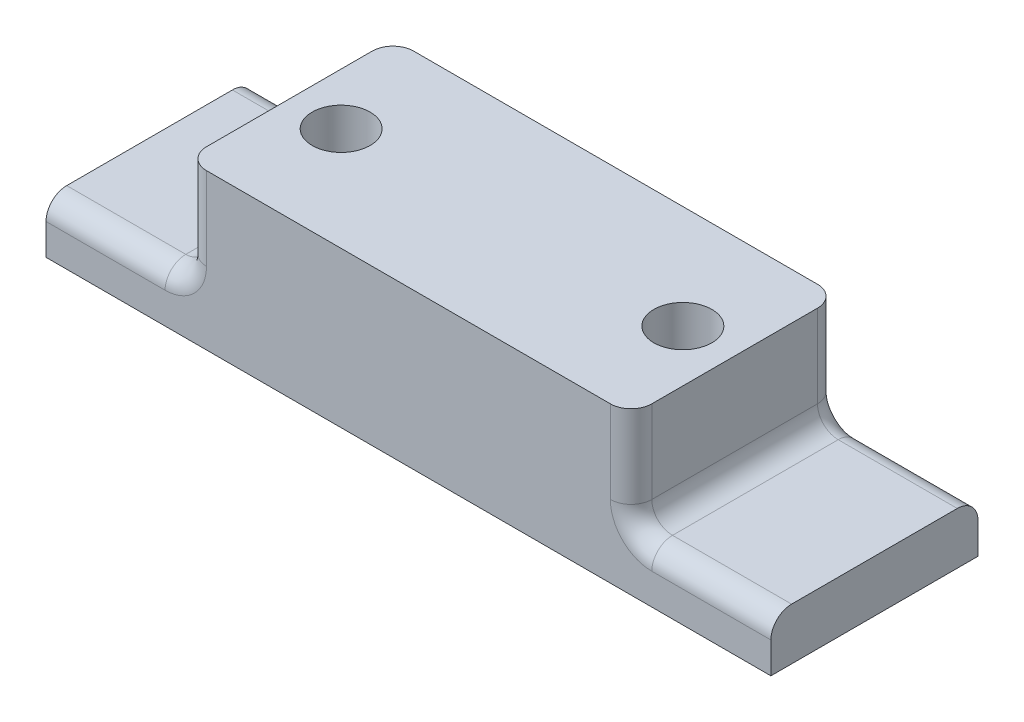
SolidWorks part; units mm, degrees
ref_plane "Front Plane" through (0, 0, 0) normal (0, 0, 1) x (1, 0, 0)
ref_plane "Top Plane" through (0, 0, 0) normal (0, 1, 0) x (1, 0, 0)
ref_plane "Right Plane" through (0, 0, 0) normal (1, 0, 0) x (0, 0, -1)
sketch "Sketch1" plane through (0, 0, 0) normal (0, 1, 0) x (1, 0, 0)
  line L0 (-29.7376, 16.1875) -> (-29.7376, -3.8125)
  line L1 (-29.7376, -3.8125) -> (40.2624, -3.8125)
  line L2 (40.2624, -3.8125) -> (40.2624, 16.1875)
  line L3 (40.2624, 16.1875) -> (-29.7376, 16.1875)
  dimension "D1" = 20
  dimension "D2" = 70
extrude "Boss-Extrude1" add sketch "Sketch1" along normal blind 5
sketch "Sketch2" plane through (0, 5, 0) normal (0, 1, 0) x (1, 0, 0)
  line L1 (-16.2376, 16.1875) -> (-16.2376, -3.8125)
  line L2 (40.2624, 16.1875) -> (-29.7376, 16.1875) construction
  line L3 (-29.7376, -3.8125) -> (40.2624, -3.8125) construction
  line L4 (-16.2376, -3.8125) -> (26.7624, -3.8125)
  line L5 (26.7624, -3.8125) -> (26.7624, 16.1875)
  line L6 (26.7624, 16.1875) -> (-16.2376, 16.1875)
  line L7 (-29.7376, 16.1875) -> (-29.7376, -3.8125) construction
  line L8 (40.2624, -3.8125) -> (40.2624, 16.1875) construction
  dimension "D1" = 13.5
  dimension "D2" = 43
  dimension "D3" = 13.5
extrude "Boss-Extrude2" add sketch "Sketch2" along normal blind 10
fillet "Fillet1" radius 2 10 edges at (33.5124, 5, -16.1875) (-22.9876, 5, -16.1875) (33.5124, 5, 3.8125) (-22.9876, 5, 3.8125) (26.7624, 10, -16.1875) (-16.2376, 10, -16.1875) (26.7624, 10, 3.8125) (-16.2376, 10, 3.8125) (-16.2376, 5, -6.1875) (26.7624, 5, -6.1875)
sketch "Sketch3" plane through (0, 15, 0) normal (0, 1, 0) x (1, 0, 0)
  line L0 (-16.2376, 6.1875) -> (26.7624, 6.1875) construction
  line L1 (-16.2376, 14.1875) -> (-16.2376, -1.8125) construction
  line L2 (26.7624, -1.8125) -> (26.7624, 14.1875) construction
  line L3 (5.2624, 6.1875) -> (5.2624, 16.1875) construction
  line L4 (24.7624, 16.1875) -> (-14.2376, 16.1875) construction
  line L5 (5.2624, 16.1875) -> (5.2624, -3.8125) construction
  line L6 (-14.2376, -3.8125) -> (24.7624, -3.8125) construction
  circle A0 centre (21.7624, 6.1875) radius 2.8
  circle A1 centre (-11.2376, 6.1875) radius 2.8
  dimension "D1" = 5
  dimension "D3" = 5.6
  dimension "D2" = 33
extrude "Cut-Extrude1" cut sketch "Sketch3" against normal through all
sketch "Sketch4" plane through (0, 0, 0) normal (0, -1, 0) x (1, 0, 0)
  line L0 (5.2624, 3.8125) -> (5.2624, -16.1875) construction
  line L1 (-8.0981, -9.9593) -> (-6.4014, -5.3544)
  line L2 (-6.4014, -5.3544) -> (-9.541, -1.5826)
  line L3 (-9.541, -1.5826) -> (-14.3772, -2.4157)
  line L4 (-14.3772, -2.4157) -> (-16.0739, -7.0205)
  line L5 (-16.0739, -7.0205) -> (-12.9343, -10.7923)
  line L6 (-12.9343, -10.7923) -> (-8.0981, -9.9593)
  line L7 (-29.7376, 3.8125) -> (40.2624, 3.8125) construction
  line L8 (40.2624, -16.1875) -> (-29.7376, -16.1875) construction
  line L9 (23.459, -10.7923) -> (18.6228, -9.9593)
  line L10 (26.5986, -7.0205) -> (23.459, -10.7923)
  line L11 (24.9019, -2.4157) -> (26.5986, -7.0205)
  line L12 (20.0657, -1.5826) -> (24.9019, -2.4157)
  line L13 (16.9261, -5.3544) -> (20.0657, -1.5826)
  line L14 (18.6228, -9.9593) -> (16.9261, -5.3544)
  circle A0 centre (-11.2376, -6.1875) radius 4.25 construction
  dimension "D1" = 8.5
extrude "Cut-Extrude2" cut sketch "Sketch4" against normal blind 8
